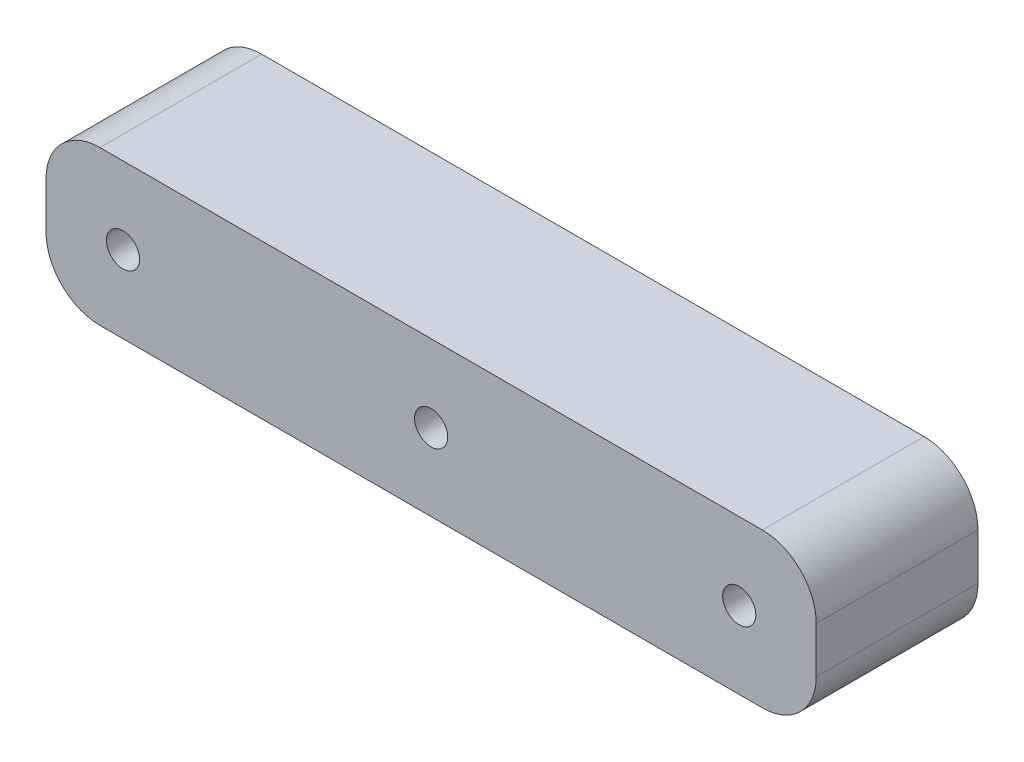
SolidWorks part; units mm, degrees
material "Balsa"
ref_plane "前视基准面" through (0, 0, 0) normal (0, 0, 1) x (1, 0, 0)
ref_plane "上视基准面" through (0, 0, 0) normal (0, 1, 0) x (1, 0, 0)
ref_plane "右视基准面" through (0, 0, 0) normal (1, 0, 0) x (0, 0, -1)
other "Configuration Table"
sketch "Sketch1" plane through (0, 0, 0) normal (0, 0, 1) x (1, 0, 0)
  line L0 (50, 0) -> (50, -20) construction
  line L1 (0, 0) -> (100, 0)
  line L2 (0, 0) -> (0, -20)
  line L3 (0, -20) -> (100, -20)
  line L4 (100, 0) -> (100, -20)
  circle A0 centre (10, -10) radius 2.15
  circle A2 centre (90, -10) radius 2.15
  circle A5 centre (50, -10) radius 2.15
  point P12 (50, -20)
  point P14 (0, -10)
  dimension "D3" = 4.3
  dimension "D4" = 80
  dimension "D5" = 4.3
  dimension "D1" = 100
  dimension "D2" = 20
extrude "Boss-Extrude1" add sketch "Sketch1" along normal blind 21
fillet "Fillet1" radius 7 4 edges at (100, 0, 10.5) (100, -20, 10.5) (0, -20, 10.5) (0, 0, 10.5)
